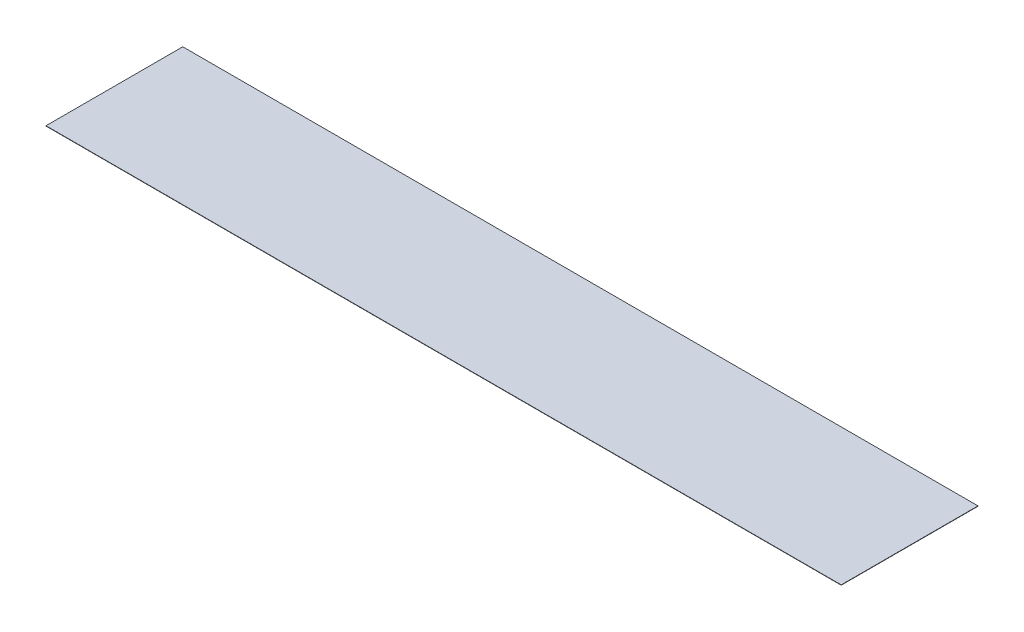
SolidWorks part; units mm, degrees
ref_plane "Plan de face" through (0, 0, 0) normal (0, 0, 1) x (1, 0, 0)
ref_plane "Plan de dessus" through (0, 0, 0) normal (0, 1, 0) x (1, 0, 0)
ref_plane "Plan de droite" through (0, 0, 0) normal (1, 0, 0) x (0, 0, -1)
sketch "Esquisse1" plane through (0, 0, 0) normal (0, 1, 0) x (1, 0, 0)
  line L1 (-250, -43) -> (250, -43)
  line L2 (-250, -43) -> (-250, 43)
  line L3 (-250, 43) -> (250, 43)
  line L4 (250, -43) -> (250, 43)
  line L5 (-250, -43) -> (250, 43) construction
  line L6 (-250, 43) -> (250, -43) construction
  point P0 (0, 0)
  dimension "D1" = 500
  dimension "D2" = 86
extrude "Boss.-Extru.1" add sketch "Esquisse1" along normal blind 0.2
